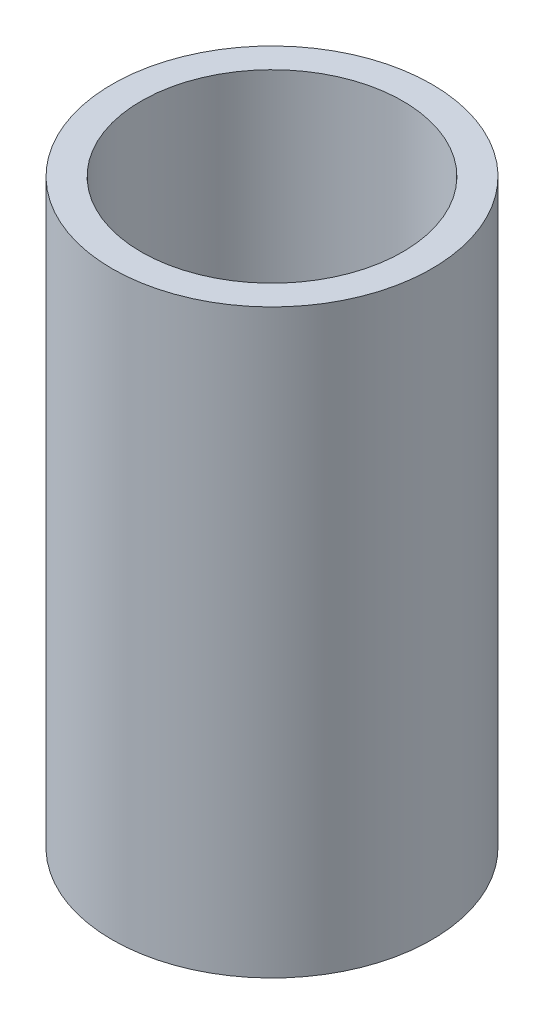
SolidWorks part; units mm, degrees
ref_plane "Front Plane" through (0, 0, 0) normal (0, 0, 1) x (1, 0, 0)
ref_plane "Top Plane" through (0, 0, 0) normal (0, 1, 0) x (1, 0, 0)
ref_plane "Right Plane" through (0, 0, 0) normal (1, 0, 0) x (0, 0, -1)
sketch "Sketch1" plane through (0, 0, 0) normal (0, 1, 0) x (1, 0, 0)
  circle A0 centre (0, 0) radius 2.25
  circle A1 centre (0, 0) radius 2.75
  dimension "D1" = 4.5
  dimension "D2" = 5.5
extrude "Boss-Extrude1" add sketch "Sketch1" along normal blind 10
